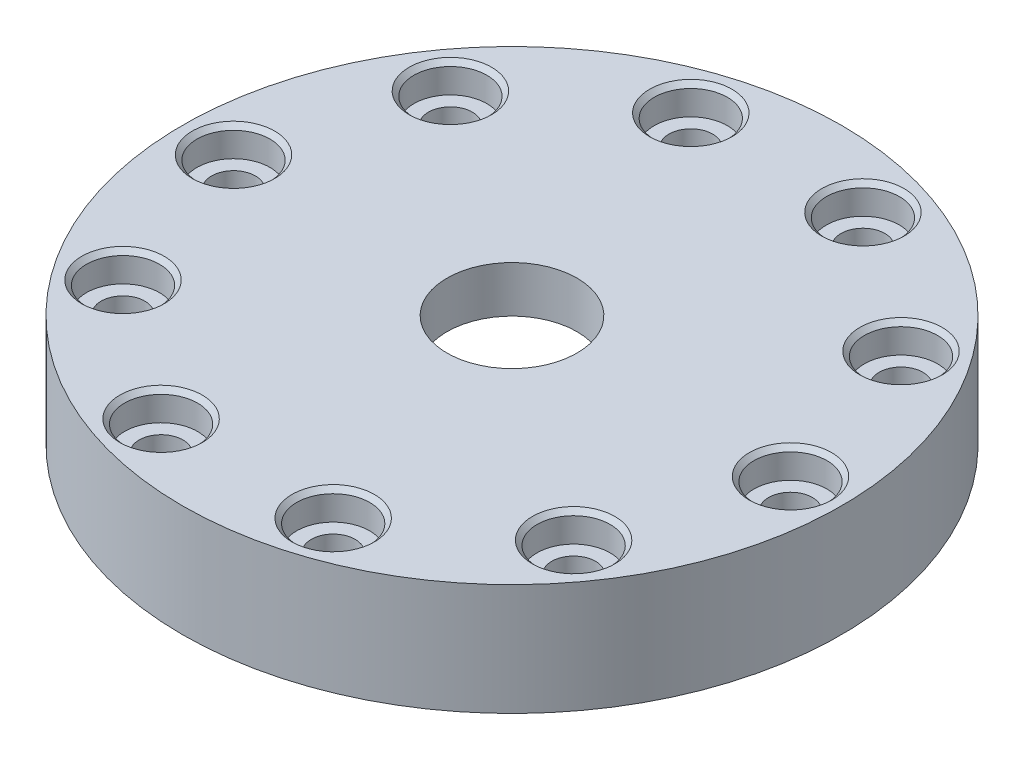
SolidWorks part; units mm, degrees
material "Nickel"
ref_plane "Front Plane" through (0, 0, 0) normal (0, 0, 1) x (1, 0, 0)
ref_plane "Top Plane" through (0, 0, 0) normal (0, 1, 0) x (1, 0, 0)
ref_plane "Right Plane" through (0, 0, 0) normal (1, 0, 0) x (0, 0, -1)
sketch "Sketch1" plane through (0, 0, 0) normal (0, 0, 1) x (1, 0, 0)
  line L0 (0, 0) -> (0, 20.7162) construction
  line L1 (8.89, 0) -> (45.085, 0)
  line L2 (8.89, 0) -> (8.89, -6.35)
  line L3 (8.89, -6.35) -> (24.13, -6.35)
  line L6 (24.13, -6.35) -> (24.13, -15.2654)
  line L7 (24.13, -15.2654) -> (45.085, -15.2654)
  line L8 (45.085, -15.2654) -> (45.085, 0)
  dimension "D1" = 6.35
  dimension "D2" = 8.89
  dimension "D4" = 8.9154
  dimension "D5" = 24.13
  dimension "D6" = 45.085
revolve "Revolve1" add sketch "Sketch1" angle 360 about L0
hole_wizard "Hole1" positions "Sketch2" profile "Sketch3" legacy end condition up to next
sketch "Sketch2" plane through (0, 0, 0) normal (0, 1, 0) x (1, 0, 0)
  line L0 (0, 0) -> (38.1, 0) construction
  point P0 (38.1, 0)
  dimension "D1" = 38.1
sketch "Sketch3" plane through (38.1, 0, 0) normal (1, 0, 0) x (0, 0, 1)
  line L0 (0, 0) -> (0, 15.2664)
  line L1 (0, 15.2664) -> (3, 15.2664)
  line L2 (3, 15.2664) -> (3, 4)
  line L3 (3, 4) -> (5, 4)
  line L4 (5, 4) -> (5, 0)
  line L5 (5, 0) -> (0, 0)
  line L6 (0, 110) -> (0, -10) construction
  dimension "Diameter" = 6
  dimension "Depth" = 15.2664
  dimension "C-Bore Diameter" = 10
  dimension "C-Bore Depth" = 4
chamfer "Chamfer1" distance 0.635 angle 45 1 edges at (38.1, 0, 5)
pattern_circular "CirPattern1" count 10 over 360 about axis through (0, 0, 0) along (0, 1, 0) of "Hole1", "Chamfer1"
fillet "Fillet1" radius 1.27 1 edges at (0, -6.35, -24.13)
